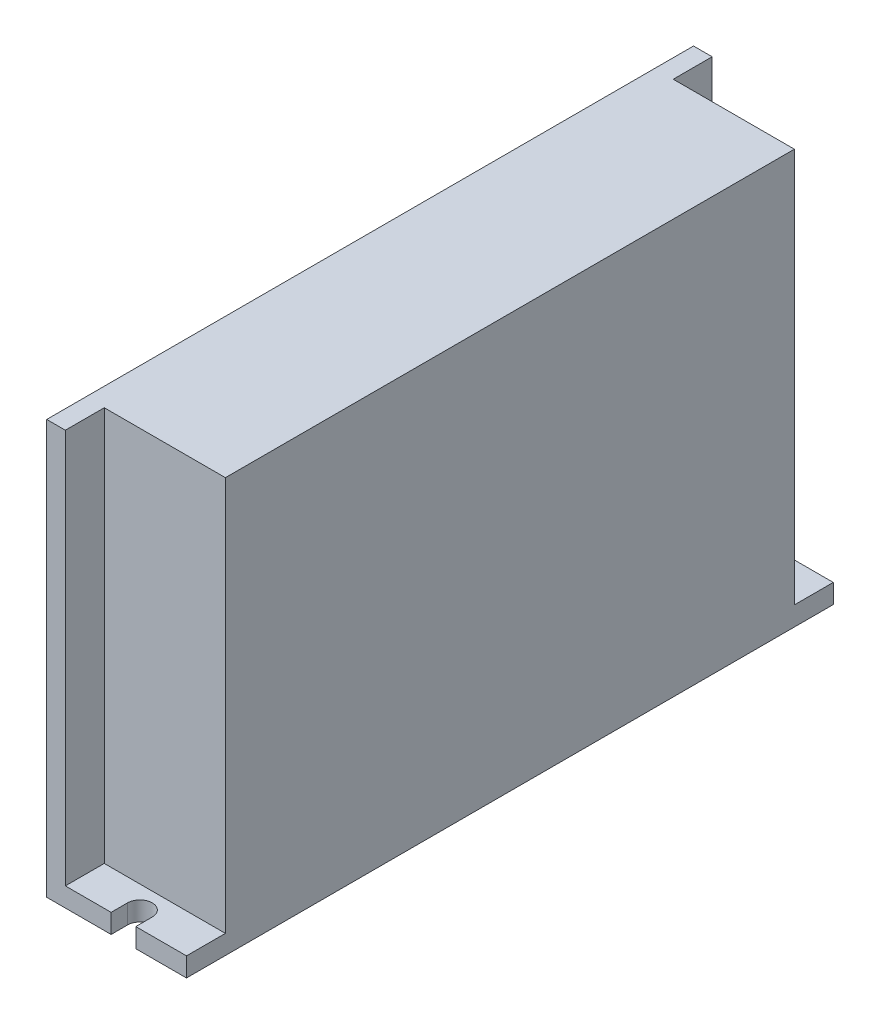
SolidWorks part; units mm, degrees
ref_plane "Front Plane" through (0, 0, 0) normal (0, 0, 1) x (1, 0, 0)
ref_plane "Top Plane" through (0, 0, 0) normal (0, 1, 0) x (1, 0, 0)
ref_plane "Right Plane" through (0, 0, 0) normal (1, 0, 0) x (0, 0, -1)
sketch "Sketch2" plane through (0, 0, 0) normal (0, 1, 0) x (1, 0, 0)
  line L1 (-12.75, -59) -> (12.75, -59)
  line L2 (-12.75, -59) -> (-12.75, 59)
  line L3 (-12.75, 59) -> (12.75, 59)
  line L4 (12.75, -59) -> (12.75, 59)
  line L5 (-12.75, -59) -> (12.75, 59) construction
  line L6 (-12.75, 59) -> (12.75, -59) construction
  point P0 (0, 0)
  dimension "D1" = 25.5
  dimension "D2" = 118
extrude "Boss-Extrude3" add sketch "Sketch2" along normal blind 3.5
sketch "Sketch3" plane through (0, 3.5, 0) normal (0, 1, 0) x (1, 0, 0)
  line L0 (12.75, 0) -> (-12.75, 0) construction
  line L1 (12.75, -59) -> (12.75, 59) construction
  line L2 (-12.75, 59) -> (-12.75, -59) construction
  line L3 (-12.75, -59) -> (12.75, -59) construction
  line L8 (-1, 56) -> (-1, 59)
  line L9 (12.75, 59) -> (-12.75, 59) construction
  line L10 (3.5, 56) -> (3.5, 59)
  line L11 (-1, -56) -> (-1, -59)
  line L12 (3.5, -56) -> (3.5, -59)
  line L13 (-1, 59) -> (3.5, 59)
  line L14 (-1, -59) -> (3.5, -59)
  arc A0 (3.5, -56) -> (-1, -56) centre (1.25, -56) ccw
  arc A1 (-1, 56) -> (3.5, 56) centre (1.25, 56) ccw
  dimension "D2" = 4.5
  dimension "D3" = 14
  dimension "D1" = 112
extrude "Cut-Extrude1" cut sketch "Sketch3" against normal through all
sketch "Sketch4" plane through (0, 3.5, 0) normal (0, 1, 0) x (1, 0, 0)
  line L0 (-12.75, -59) -> (-1, -59) construction
  line L1 (-12.75, 59) -> (-9.35, 59)
  line L2 (-12.75, 59) -> (-12.75, -59)
  line L3 (-12.75, -59) -> (-9.35, -59)
  line L4 (-9.35, 59) -> (-9.35, -59)
  dimension "D1" = 3.4
extrude "Boss-Extrude4" add sketch "Sketch4" along normal blind 72
sketch "Sketch5" plane through (0, 3.5, 0) normal (0, 1, 0) x (1, 0, 0)
  line L0 (12.75, 0) -> (-9.35, 0) construction
  line L1 (12.75, -59) -> (12.75, 59) construction
  line L2 (-9.35, -59) -> (-9.35, 59) construction
  line L3 (12.75, 59) -> (3.5, 59) construction
  line L4 (-9.35, -51.9) -> (12.75, -51.9)
  line L5 (-9.35, -51.9) -> (-9.35, 51.9)
  line L6 (-9.35, 51.9) -> (12.75, 51.9)
  line L7 (12.75, -51.9) -> (12.75, 51.9)
  line L8 (-9.35, -51.9) -> (12.75, 51.9) construction
  line L9 (-9.35, 51.9) -> (12.75, -51.9) construction
  point P6 (1.7, 0)
  dimension "D1" = 7.1
extrude "Boss-Extrude5" add sketch "Sketch5" along normal blind 72
sketch "Sketch6" plane through (0, 75.5, 0) normal (0, 1, 0) x (1, 0, 0)
  line L1 (-7.6401, 46.247) -> (5.0392, 46.247)
  line L2 (-7.6401, 46.247) -> (-7.6401, 26.9029)
  line L3 (-7.6401, 26.9029) -> (5.0392, 26.9029)
  line L4 (5.0392, 46.247) -> (5.0392, 26.9029)
